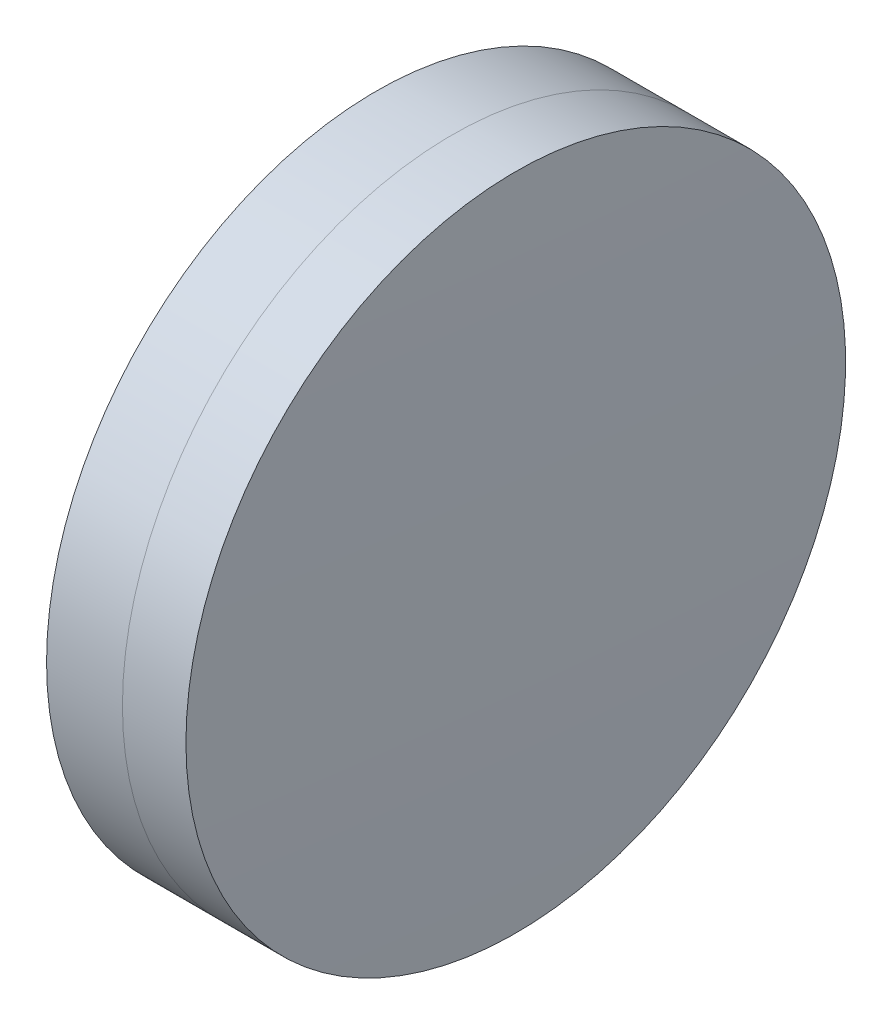
SolidWorks part; units mm, degrees
ref_plane "前视基准面" through (0, 0, 0) normal (0, 0, 1) x (1, 0, 0)
ref_plane "上视基准面" through (0, 0, 0) normal (0, 1, 0) x (1, 0, 0)
ref_plane "右视基准面" through (0, 0, 0) normal (1, 0, 0) x (0, 0, -1)
sketch "草图1" plane through (0, 0, 0) normal (0, 1, 0) x (1, 0, 0)
  line L0 (235.8075, 0) -> (325.7682, 0) construction
  line L1 (314.4883, -12.7) -> (317.41, -12.7)
  line L2 (314.4883, 12.7) -> (317.41, 12.7)
  arc A0 (317.41, -12.7) -> (317.41, 12.7) centre (180.8994, 0) ccw
  arc A1 (314.4883, 12.7) -> (314.4883, -12.7) centre (479.1994, 0) ccw
  point P4 (325.7682, 0)
  point P10 (313.9994, 0)
  point P11 (317.9994, 0)
  dimension "D3" = 165.2
  dimension "D4" = 137.1
  dimension "D1" = 12.7
  dimension "D2" = 12.7
  dimension "D5" = 4
revolve "旋转1" add sketch "草图1" angle 360 about L0
sketch "草图2" plane through (0, 0, 0) normal (0, 1, 0) x (1, 0, 0)
  line L0 (-0.5519, 0) -> (328.5936, 0) construction
  line L2 (317.41, 12.7) -> (319.8547, 12.7)
  line L3 (317.41, -12.7) -> (319.8547, -12.7)
  arc A0 (319.8547, -12.7) -> (319.8547, 12.7) centre (-237.4006, 0) ccw
  arc A1 (317.41, -12.7) -> (317.41, 12.7) centre (180.8994, 0) ccw construction
  arc A2 (317.41, -12.7) -> (317.41, 12.7) centre (180.8994, 0) ccw
  point P4 (317.9994, 0)
  point P8 (319.9994, 0)
  point P9 (328.5936, 0)
  dimension "D1" = 557.4
  dimension "D2" = 2
revolve "旋转3" add sketch "草图2" angle 360 about L0
